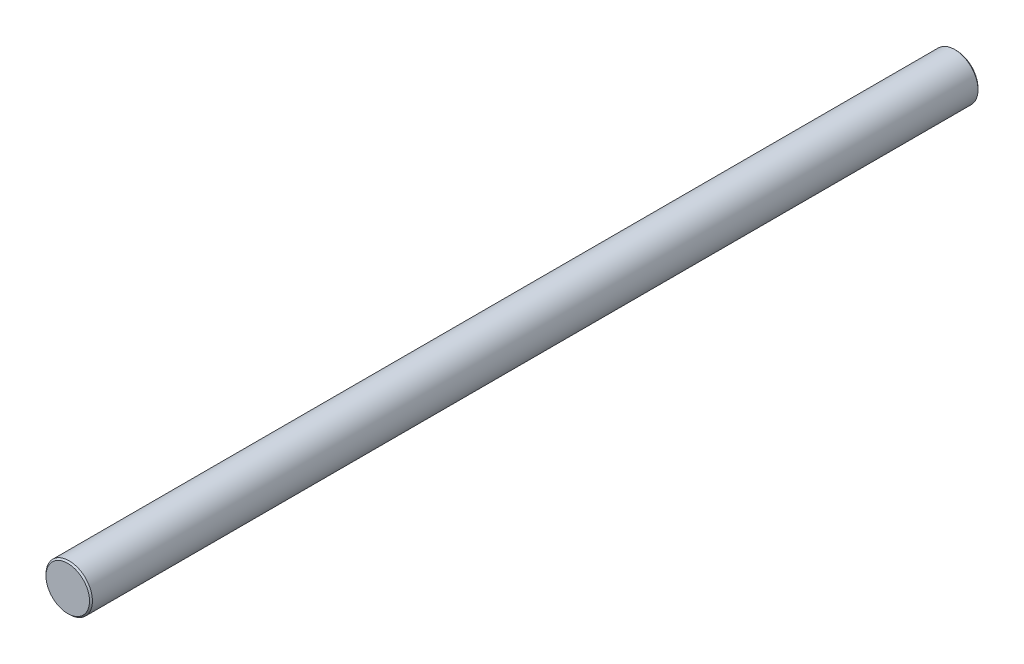
SolidWorks part; units mm, degrees
material "1023 Carbon Steel Sheet (SS)"
ref_plane "Front Plane" through (0, 0, 0) normal (0, 0, 1) x (1, 0, 0)
ref_plane "Top Plane" through (0, 0, 0) normal (0, 1, 0) x (1, 0, 0)
ref_plane "Right Plane" through (0, 0, 0) normal (1, 0, 0) x (0, 0, -1)
sketch "Sketch1" plane through (0, 0, 0) normal (0, 0, 1) x (1, 0, 0)
  circle A0 centre (0, 0) radius 8
  dimension "D1" = 16
extrude "Boss-Extrude1" add sketch "Sketch1" along normal blind 306
chamfer "Chamfer1" distance 0.5 angle 45 2 edges at (8, 0, 0) (8, 0, 306)
